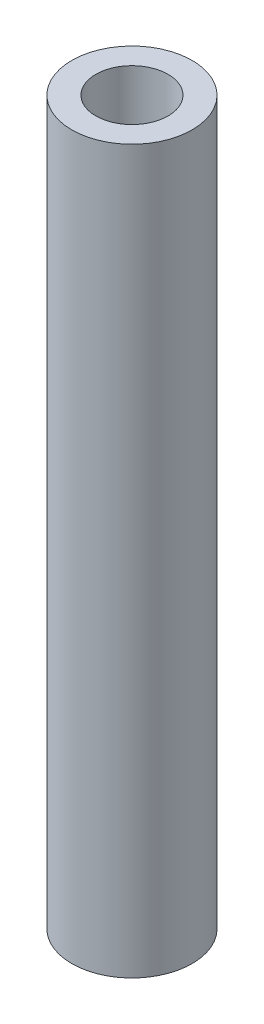
SolidWorks part; units mm, degrees
material "6061 合金"
ref_plane "前视基准面" through (0, 0, 0) normal (0, 0, 1) x (1, 0, 0)
ref_plane "上视基准面" through (0, 0, 0) normal (0, 1, 0) x (1, 0, 0)
ref_plane "右视基准面" through (0, 0, 0) normal (1, 0, 0) x (0, 0, -1)
sketch "草图1" plane through (0, 0, 0) normal (0, 1, 0) x (1, 0, 0)
  circle A0 centre (0, 0) radius 1.5
  circle A1 centre (0, 0) radius 2.5
  dimension "D1" = 3
  dimension "D2" = 5
extrude "凸台-拉伸1" add sketch "草图1" along normal blind 30
